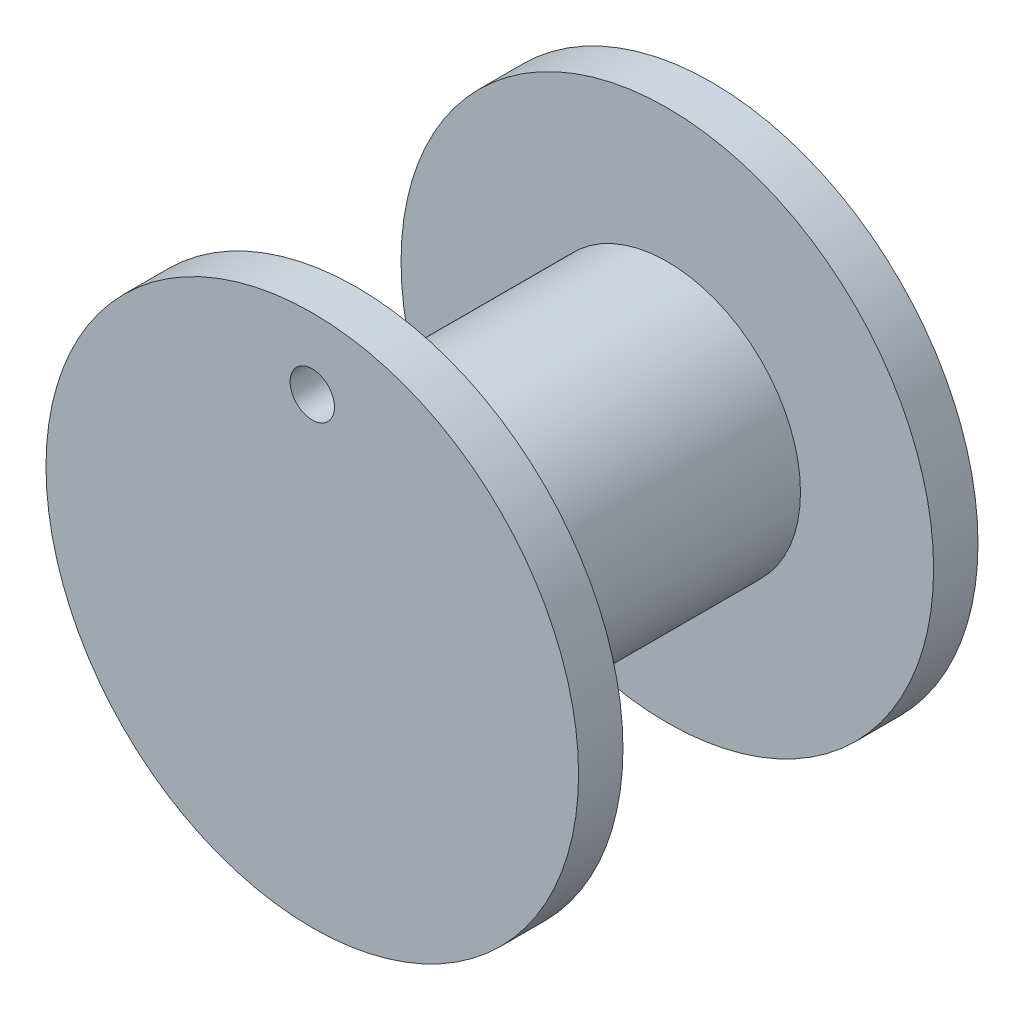
SolidWorks part; units mm, degrees
ref_plane "Front Plane" through (0, 0, 0) normal (0, 0, 1) x (1, 0, 0)
ref_plane "Top Plane" through (0, 0, 0) normal (0, 1, 0) x (1, 0, 0)
ref_plane "Right Plane" through (0, 0, 0) normal (1, 0, 0) x (0, 0, -1)
sketch "Sketch1" plane through (0, 0, 0) normal (0, 0, 1) x (1, 0, 0)
  line L1 (7.3323, 0) -> (3.6662, 6.35)
  line L2 (3.6662, 6.35) -> (-3.6662, 6.35)
  line L3 (-3.6662, 6.35) -> (-7.3323, 0)
  line L4 (-7.3323, 0) -> (-3.6662, -6.35)
  line L5 (-3.6662, -6.35) -> (3.6662, -6.35)
  line L6 (3.6662, -6.35) -> (7.3323, 0)
  circle A0 centre (0, 0) radius 6.35 construction
  circle A1 centre (0, 0) radius 19.05
  dimension "D2" = 38.1
  dimension "D1" = 12.7
extrude "Boss-Extrude1" add sketch "Sketch1" along normal blind 3.175
sketch "Sketch2" plane through (0, 0, 3.175) normal (0, 0, 1) x (1, 0, 0)
  line L1 (7.3323, 0) -> (3.6662, 6.35)
  line L2 (3.6662, 6.35) -> (-3.6662, 6.35)
  line L3 (-3.6662, 6.35) -> (-7.3323, 0)
  line L4 (-7.3323, 0) -> (-3.6662, -6.35)
  line L5 (-3.6662, -6.35) -> (3.6662, -6.35)
  line L6 (3.6662, -6.35) -> (7.3323, 0)
  circle A0 centre (0, 0) radius 9.525
  circle A1 centre (0, 0) radius 6.35 construction
  dimension "D1" = 19.05
  dimension "D2" = 12.7
extrude "Boss-Extrude2" add sketch "Sketch2" along normal blind 22.225
sketch "Sketch3" plane through (0, 0, 25.4) normal (0, 0, 1) x (1, 0, 0)
  circle A0 centre (0, 0) radius 19.05
  circle A1 centre (0, 13.9958) radius 1.5875
  dimension "D1" = 38.1
  dimension "D2" = 3.175
extrude "Boss-Extrude3" add sketch "Sketch3" along normal blind 3.175
